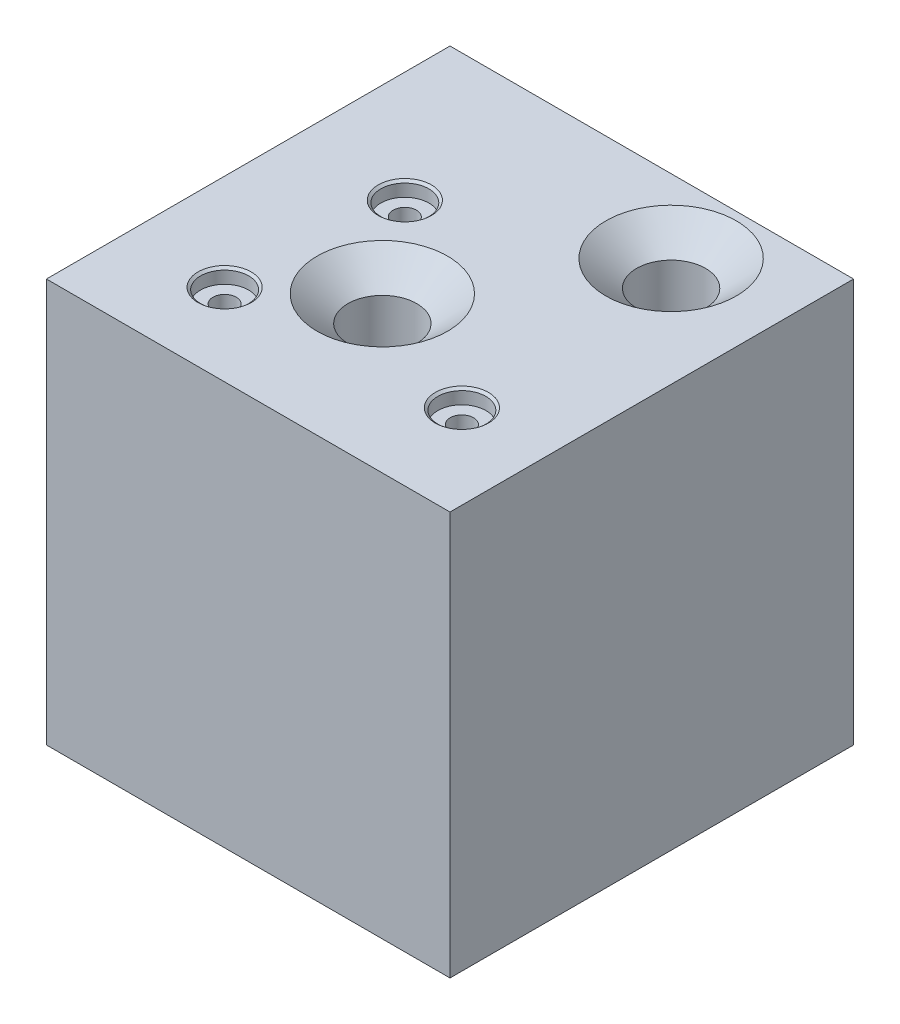
SolidWorks part; units mm, degrees
ref_plane "Front Plane" through (0, 0, 0) normal (0, 0, 1) x (1, 0, 0)
ref_plane "Top Plane" through (0, 0, 0) normal (0, 1, 0) x (1, 0, 0)
ref_plane "Right Plane" through (0, 0, 0) normal (1, 0, 0) x (0, 0, -1)
sketch "Sketch1" plane through (0, 0, 0) normal (0, 1, 0) x (1, 0, 0)
  line L1 (50, -50) -> (-50, -50)
  line L2 (50, -50) -> (50, 50)
  line L3 (50, 50) -> (-50, 50)
  line L4 (-50, -50) -> (-50, 50)
  line L5 (50, -50) -> (-50, 50) construction
  line L6 (50, 50) -> (-50, -50) construction
  point P0 (0, 0)
  dimension "D1" = 100
extrude "Boss-Extrude1" add sketch "Sketch1" along normal mid plane 100
sketch "Sketch2" plane through (0, 50, 0) normal (0, 1, 0) x (1, 0, 0)
  point P0 (-26.1569, -29.6916)
  point P1 (29.1025, -26.1569)
  point P2 (-5.2315, -11.5322)
  point P3 (-22.5043, 11.3111)
  point P4 (22.9756, 31.8124)
  point P5 (-5.2315, -11.5322)
sketch "Sketch5" plane through (0, 50, 0) normal (0, 1, 0) x (1, 0, 0)
  point P0 (22.9756, 31.8124)
  point P3 (-5.2315, -11.5322)
hole_wizard "CSK for M2 Flat Head Machine Screw1" positions "Sketch5" profile "Sketch6" countersink size "M2" standard "ANSI Metric"
sketch "Sketch6" plane through (22.9756, 50, -31.8124) normal (1, 0, 0) x (0, 0, 1)
  line L0 (0, 0) -> (0, 55.9283)
  line L1 (0, 55.9283) -> (8.535, 50.8)
  line L2 (8.535, 50.8) -> (8.535, 6.3939)
  line L3 (8.535, 6.3939) -> (16.155, 0)
  line L5 (16.155, 0) -> (0, 0)
  line L6 (-8.535, 6.3939) -> (-16.155, 0) construction
  line L10 (0, 55.9283) -> (-8.535, 50.8) construction
  line L11 (0, -6.35) -> (0, 107.95) construction
  dimension "Hole Dia." = 17.07
  dimension "Hole Depth" = 50.8
  dimension "Near C'Sink Dia." = 32.31
  dimension "Near C'Sink Angle" = 100
  dimension "Drill Angle" = 118
sketch "Sketch9" plane through (0, 50, 0) normal (0, 1, 0) x (1, 0, 0)
  point P0 (-22.5043, 11.3111)
  point P3 (-26.1569, -29.6916)
  point P6 (29.1025, -26.1569)
hole_wizard "CBORE for M5 Hex Head Bolt1" positions "Sketch9" profile "Sketch10" counterbore size "M5" standard "ANSI Metric" end condition through all
sketch "Sketch10" plane through (-22.5043, 50, -11.3111) normal (1, 0, 0) x (0, 0, 1)
  line L0 (0, 0) -> (0, 100)
  line L1 (0, 100) -> (2.895, 100)
  line L3 (2.895, 100) -> (2.895, 3.58)
  line L4 (5.955, 3.58) -> (2.895, 3.58)
  line L5 (5.955, 3.58) -> (5.955, 0.5328)
  line L6 (5.955, 0.5328) -> (6.59, 0)
  line L7 (6.59, 0) -> (0, 0)
  line L8 (-5.955, 0.5328) -> (-6.59, 0) construction
  line L11 (0, -6.35) -> (0, 107.95) construction
  dimension "Thru Hole Dia." = 5.79
  dimension "Thru Hole Depth" = 100
  dimension "C'Bore Dia." = 11.91
  dimension "C'Bore Depth" = 3.58
  dimension "Near C'Sink Dia." = 13.18
  dimension "Near C'Sink Angle" = 100
